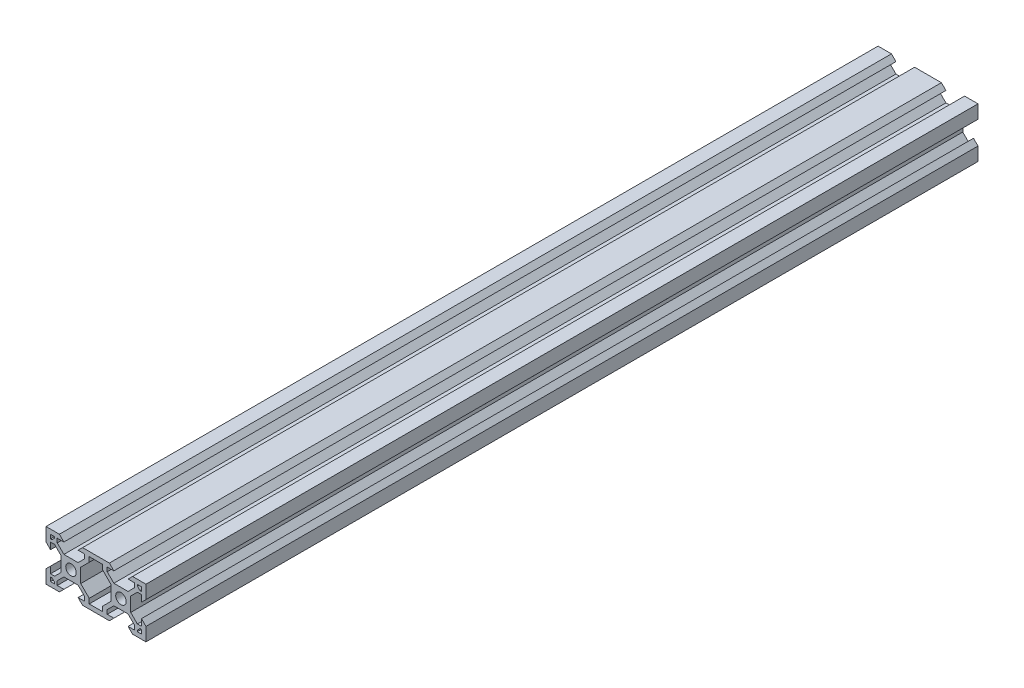
SolidWorks part; units mm, degrees
ref_plane "Front Plane" through (0, 0, 0) normal (0, 0, 1) x (1, 0, 0)
ref_plane "Top Plane" through (0, 0, 0) normal (0, 1, 0) x (1, 0, 0)
ref_plane "Right Plane" through (0, 0, 0) normal (1, 0, 0) x (0, 0, -1)
sketch "Sketch1" plane through (0, 0, 0) normal (0, 0, 1) x (1, 0, 0)
  line L0 (0, 0) -> (0, 5.36)
  line L1 (0, 20) -> (5.36, 20)
  line L3 (20, 0) -> (14.64, 0)
  line L4 (0, 10) -> (20, 10) construction
  line L5 (5.36, 0) -> (0, 0)
  line L6 (4.5007, 18.2) -> (7.16, 18.2)
  line L7 (17.3007, 3.76) -> (17.3007, 1.8)
  line L8 (15.4993, 1.8) -> (12.84, 1.8)
  line L9 (20, 0) -> (0, 0) construction
  line L10 (7.16, 1.8) -> (4.5007, 1.8)
  line L11 (15.4993, 3.44) -> (12.84, 6.0993)
  line L12 (4.5007, 16.56) -> (7.16, 13.9007)
  line L13 (13.9007, 12.84) -> (13.9007, 7.16)
  line L14 (12.84, 13.9007) -> (7.16, 13.9007)
  line L15 (6.0993, 12.84) -> (6.0993, 7.16)
  line L16 (7.16, 6.0993) -> (12.84, 6.0993)
  line L17 (4.5007, 16.56) -> (4.5007, 18.2)
  line L18 (3.44, 15.4993) -> (1.8, 15.4993)
  line L19 (4.5007, 3.44) -> (4.5007, 1.8)
  line L20 (3.44, 4.5007) -> (1.8, 4.5007)
  line L21 (15.4993, 3.44) -> (15.4993, 1.8)
  line L23 (17.3007, 1.8) -> (22.7007, 1.8)
  line L24 (15.4993, 16.56) -> (15.4993, 18.2)
  line L25 (7.16, 18.2) -> (5.36, 20)
  line L26 (12.84, 1.8) -> (14.64, 0)
  line L27 (7.16, 1.8) -> (5.36, 0)
  line L28 (12.84, 18.2) -> (14.64, 20)
  line L29 (1.8, 7.16) -> (0, 5.36)
  line L30 (1.8, 12.84) -> (0, 14.64)
  line L31 (22.7007, 1.8) -> (22.7007, 3.76)
  line L32 (17.3007, 16.24) -> (17.3007, 18.2)
  line L33 (17.3007, 18.2) -> (22.6993, 18.2)
  line L34 (22.6993, 18.2) -> (22.6993, 16.24)
  line L35 (38.2013, 12.8423) -> (40.001, 14.6427)
  line L36 (38.2024, 7.1623) -> (40.0028, 5.3627)
  line L37 (27.16, 18.2) -> (25.36, 20)
  line L38 (32.84, 1.8) -> (34.64, 0)
  line L39 (27.16, 1.8) -> (25.36, 0)
  line L40 (32.84, 18.2) -> (34.64, 20)
  line L41 (24.5013, 16.5597) -> (24.5009, 18.2)
  line L42 (1.8, 18.2) -> (3.4307, 18.2)
  line L43 (3.4307, 18.2) -> (3.4307, 17.63)
  line L44 (24.5038, 3.4397) -> (24.5041, 1.8)
  line L45 (36.5629, 4.5027) -> (38.2029, 4.503)
  line L46 (35.5025, 3.4418) -> (35.5028, 1.8)
  line L47 (36.5608, 15.5014) -> (38.2008, 15.5017)
  line L48 (35.4999, 16.5618) -> (35.4996, 18.2)
  line L49 (32.8426, 6.1006) -> (27.1626, 6.0995)
  line L50 (33.902, 12.8415) -> (33.9031, 7.1615)
  line L51 (27.1611, 13.9009) -> (32.8411, 13.902)
  line L52 (26.1007, 12.84) -> (26.1007, 7.16)
  line L53 (1.8, 4.5007) -> (1.8, 7.16)
  line L54 (24.5038, 3.4397) -> (27.1626, 6.0995)
  line L55 (35.5025, 3.4418) -> (32.8426, 6.1006)
  line L56 (36.5629, 4.5027) -> (33.9031, 7.1615)
  line L57 (24.5041, 1.8) -> (27.16, 1.8)
  line L58 (3.4307, 17.63) -> (2.37, 16.5693)
  line L59 (3.44, 4.5007) -> (6.0993, 7.16)
  line L60 (35.4996, 18.2) -> (32.84, 18.2)
  line L61 (20, 0) -> (25.36, 0)
  line L62 (39.9999, 20) -> (34.64, 20)
  line L63 (40.0038, 0) -> (40.0028, 5.3627)
  line L64 (1.8, 12.84) -> (1.8, 15.4993)
  line L65 (1.8, 1.8) -> (1.8, 18.2) construction
  line L66 (0, 14.64) -> (0, 20)
  line L67 (0, 0) -> (0, 20) construction
  line L68 (14.64, 20) -> (20, 20)
  line L69 (0, 20) -> (20, 20) construction
  line L70 (12.84, 18.2) -> (15.4993, 18.2)
  line L71 (1.8, 18.2) -> (18.2, 18.2) construction
  line L72 (25.36, 20) -> (20, 20)
  line L73 (27.16, 18.2) -> (24.5009, 18.2)
  line L74 (38.2013, 12.8423) -> (38.2008, 15.5017)
  line L75 (40.001, 14.6427) -> (39.9999, 20)
  line L76 (32.84, 1.8) -> (35.5028, 1.8)
  line L77 (34.64, 0) -> (40.0038, 0)
  line L78 (38.2029, 4.503) -> (38.2024, 7.1623)
  line L79 (35.4999, 16.5618) -> (32.8411, 13.902)
  line L80 (4.5007, 3.44) -> (7.16, 6.0993)
  line L81 (2.37, 16.5693) -> (1.8, 16.5693)
  line L82 (18.2, 1.8) -> (1.8, 1.8) construction
  line L83 (18.2, 18.2) -> (18.2, 1.8) construction
  line L84 (1.8, 16.5693) -> (1.8, 18.2)
  line L85 (20, 20) -> (20, 0) construction
  line L86 (1.8, 3.4307) -> (1.8, 1.8)
  line L87 (2.37, 3.4307) -> (1.8, 3.4307)
  line L88 (3.4307, 2.37) -> (2.37, 3.4307)
  line L89 (3.4307, 1.8) -> (3.4307, 2.37)
  line L90 (1.8, 1.8) -> (3.4307, 1.8)
  line L91 (13.9007, 7.16) -> (17.3007, 3.76)
  line L92 (20, 20) -> (20, -0.3542) construction
  line L93 (38.2, 1.8) -> (36.5693, 1.8)
  line L94 (36.5693, 1.8) -> (36.5693, 2.37)
  line L95 (36.5693, 2.37) -> (37.63, 3.4307)
  line L96 (37.63, 3.4307) -> (38.2, 3.4307)
  line L97 (38.2, 3.4307) -> (38.2, 1.8)
  line L98 (38.2, 16.5693) -> (38.2, 18.2)
  line L99 (37.63, 16.5693) -> (38.2, 16.5693)
  line L100 (36.5693, 17.63) -> (37.63, 16.5693)
  line L101 (36.5693, 18.2) -> (36.5693, 17.63)
  line L102 (38.2, 18.2) -> (36.5693, 18.2)
  line L103 (6.0993, 12.84) -> (3.44, 15.4993)
  line L104 (13.9007, 12.84) -> (17.3007, 16.24)
  line L105 (12.84, 13.9007) -> (15.4993, 16.56)
  line L106 (33.902, 12.8415) -> (36.5608, 15.5014)
  line L108 (27.1611, 13.9009) -> (24.5013, 16.5597)
  line L109 (26.1007, 12.84) -> (22.6993, 16.24)
  line L110 (26.1007, 7.16) -> (22.7007, 3.76)
  circle A0 centre (10, 10) radius 2.1
  circle A1 centre (30, 10) radius 2.1
  point P14 (17.3007, 3.76)
  point P81 (0, 0)
  point P82 (0, 0)
  point P112 (17.3007, 1.8)
  dimension "D3" = 4.2
  dimension "D1" = 20
  dimension "D2" = 20
  dimension "D5" = 5.4
  dimension "D7" = 1.07
  dimension "D8" = 45
  dimension "D9" = 1.5
  dimension "D10" = 4.5007
  dimension "D11" = 5.68
  dimension "D12" = 5.68
  dimension "D13" = 5.68
  dimension "D14" = 5.68
  dimension "D15" = 1.64
  dimension "D16" = 1.64
  dimension "D17" = 1.64
  dimension "D18" = 1.64
  dimension "D19" = 1.64
  dimension "D20" = 15.4993
  dimension "D21" = 1.07
  dimension "D22" = 1.64
  dimension "D23" = 45
  dimension "D24" = 45
  dimension "D25" = 1.5
  dimension "D26" = 45
  dimension "D27" = 45
  dimension "D28" = 45
  dimension "D4" = 1.8
extrude "Boss-Extrude1" add sketch "Sketch1" against normal blind 333
